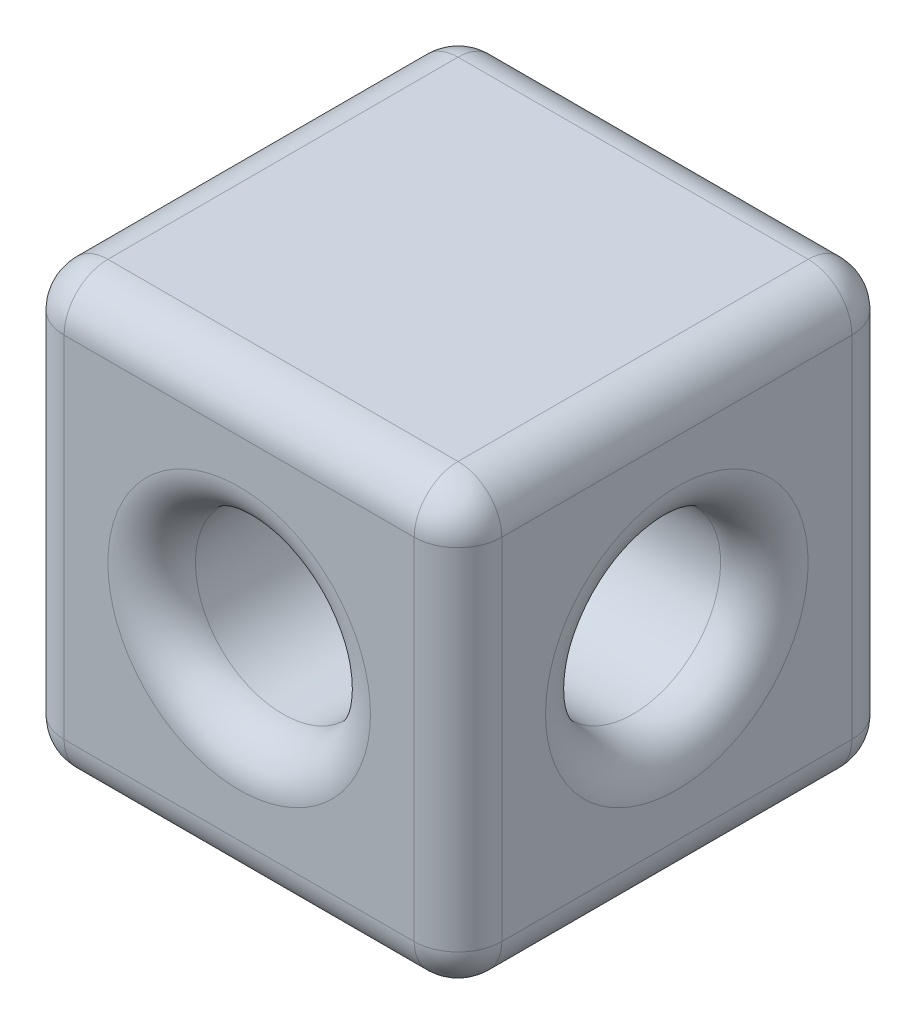
SolidWorks part; units mm, degrees
material "Hexcel AS4C (3000 Filaments)"
ref_plane "Plan de face" through (0, 0, 0) normal (0, 0, 1) x (1, 0, 0)
ref_plane "Plan de dessus" through (0, 0, 0) normal (0, 1, 0) x (1, 0, 0)
ref_plane "Plan de droite" through (0, 0, 0) normal (1, 0, 0) x (0, 0, -1)
sketch "Esquisse1" plane through (0, 0, 0) normal (0, 0, 1) x (1, 0, 0)
  line L1 (-2.5, -2.5) -> (2.5, -2.5)
  line L2 (-2.5, -2.5) -> (-2.5, 2.5)
  line L3 (-2.5, 2.5) -> (2.5, 2.5)
  line L4 (2.5, -2.5) -> (2.5, 2.5)
  line L5 (-2.5, -2.5) -> (2.5, 2.5) construction
  line L6 (-2.5, 2.5) -> (2.5, -2.5) construction
  circle A0 centre (0, 0) radius 1
  point P0 (0, 0)
  dimension "D3" = 2
  dimension "D1" = 5
  dimension "D2" = 5
extrude "Boss.-Extru.1" add sketch "Esquisse1" along normal blind 5
sketch "Esquisse2" plane through (2.5, 0, 0) normal (1, 0, 0) x (0, 0, -1)
  line L0 (0, 2.5) -> (-5, -2.5) construction
  line L1 (-5, -2.5) -> (-5, 2.5) construction
  line L2 (-5, -2.5) -> (0, -2.5) construction
  line L3 (-5, -2.5) -> (-5, 2.5) construction
  line L4 (-5, 2.5) -> (0, -2.5) construction
  circle A0 centre (-2.5, 0) radius 1
  dimension "D1" = 2
extrude "Enlèv. mat.-Extru.1" cut sketch "Esquisse2" against normal blind 10
fillet "Congé1" radius 0.5 16 edges at (-2.5, -2.5, 2.5) (-2.5, 0, 1.5) (1, 0, 5) (0, -2.5, 5) (-2.5, 0, 5) (0, 2.5, 5) (-2.5, 2.5, 2.5) (2.5, -2.5, 2.5) (2.5, 0, 5) (2.5, 2.5, 2.5) (2.5, 0, 1.5) (1, 0, 0) (0, 2.5, 0) (-2.5, 0, 0) (0, -2.5, 0) (2.5, 0, 0)
